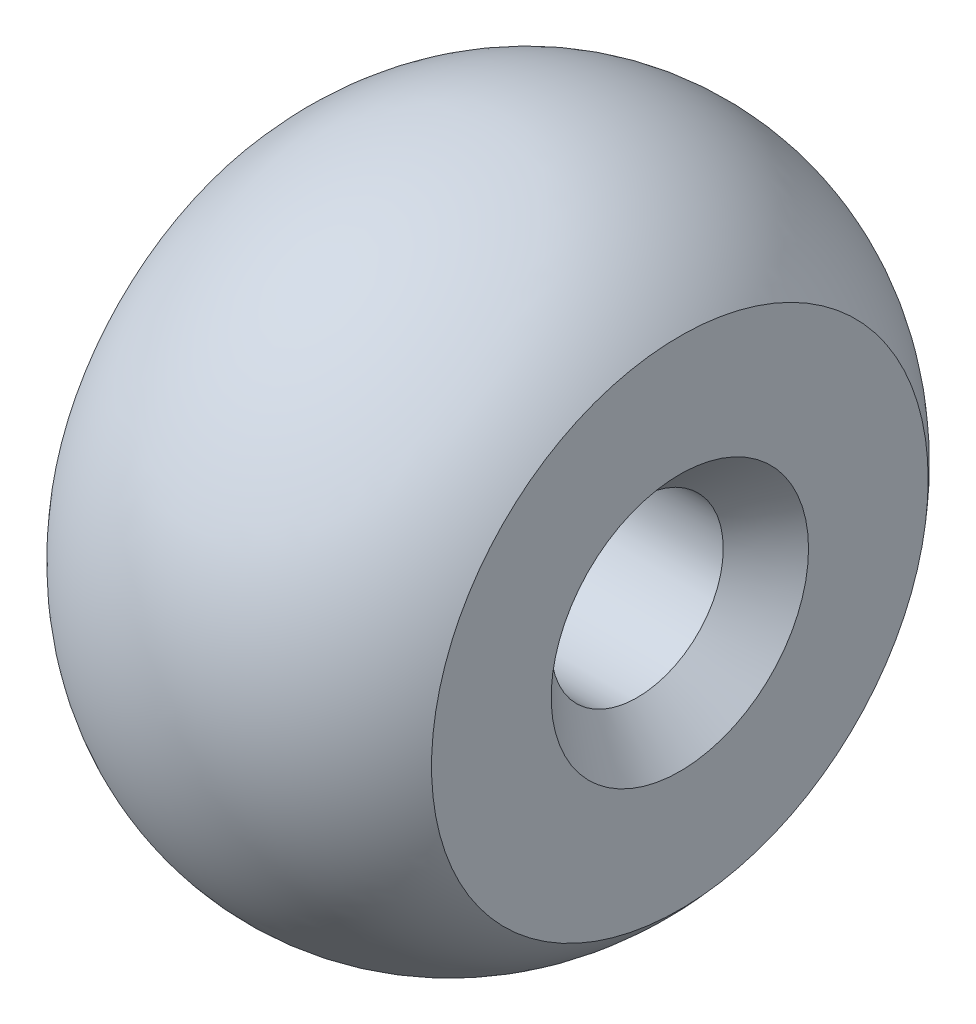
SolidWorks part; units mm, degrees
ref_plane "Ön Düzlem" through (0, 0, 0) normal (0, 0, 1) x (1, 0, 0)
ref_plane "Üst Düzlem" through (0, 0, 0) normal (0, 1, 0) x (1, 0, 0)
ref_plane "Sağ Düzlem" through (0, 0, 0) normal (1, 0, 0) x (0, 0, -1)
sketch "Çizim1" plane through (0, 0, 0) normal (0, 0, 1) x (1, 0, 0)
  line L0 (0, 1.9818) -> (-8.6484, 1.9818) construction
  line L1 (0, 1.9818) -> (11.4727, 1.9818) construction
  line L2 (0, 4) -> (4.5, 4)
  line L3 (0, 4) -> (-4.5, 4)
  line L4 (-4.5, 4) -> (-4.5, 7.8065)
  line L5 (4.5, 4) -> (4.5, 7.8065)
  arc A0 (-4.5, 7.8065) -> (4.5, 7.8065) centre (0, 3.9818) cw
  point P11 (0, 4)
  dimension "D2" = 9
revolve "Döndür2" add sketch "Çizim1" angle 360 about L0
chamfer "Pah1" distance 1 angle 45 1 edges at (4.5, 1.9818, -2.0182)
